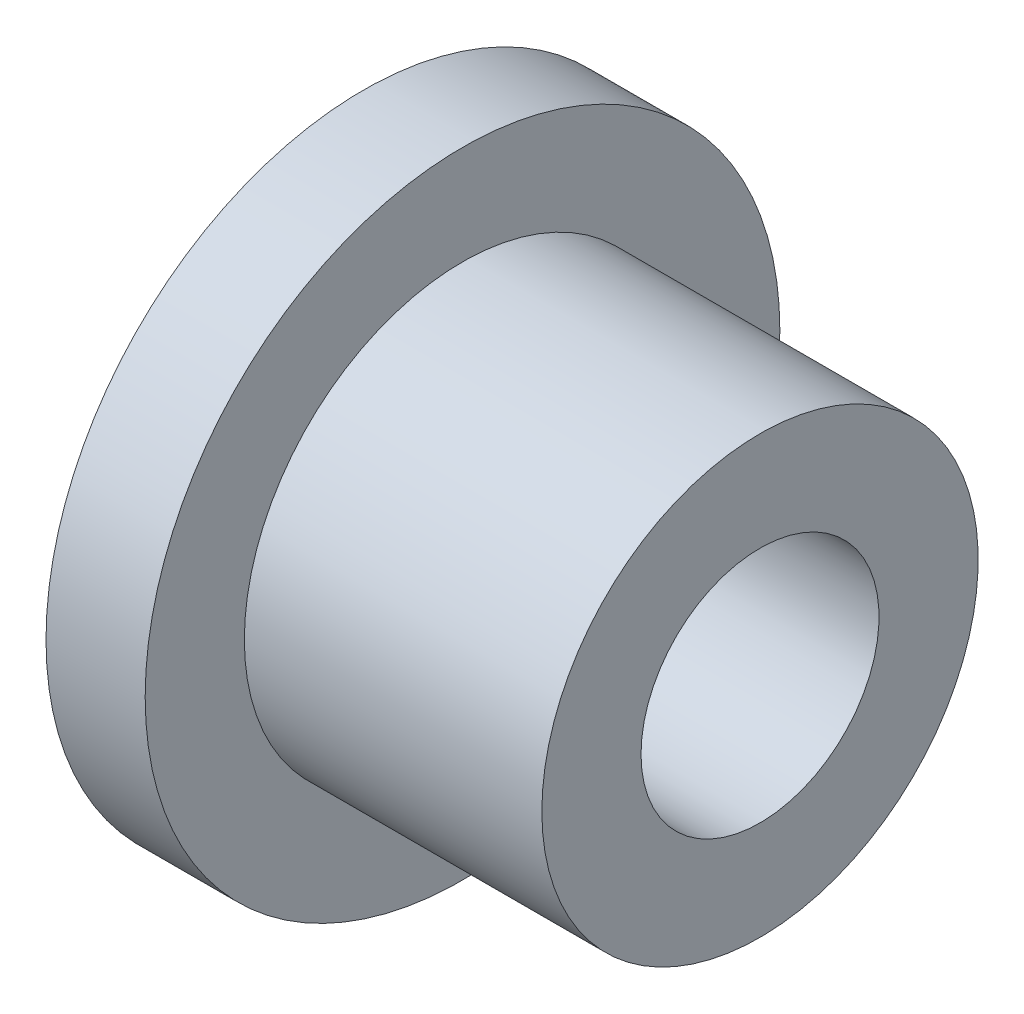
SolidWorks part; units mm, degrees
ref_plane "Front Plane" through (0, 0, 0) normal (0, 0, 1) x (1, 0, 0)
ref_plane "Top Plane" through (0, 0, 0) normal (0, 1, 0) x (1, 0, 0)
ref_plane "Right Plane" through (0, 0, 0) normal (1, 0, 0) x (0, 0, -1)
other "Configuration Table"
sketch "Sketch1" plane through (0, 0, 0) normal (0, 0, 1) x (1, 0, 0)
  line L0 (0, 6) -> (0, 16)
  line L1 (0, 16) -> (5, 16)
  line L2 (5, 16) -> (5, 11)
  line L3 (5, 11) -> (20, 11)
  line L4 (20, 11) -> (20, 6)
  line L5 (20, 6) -> (0, 6)
  line L6 (-20, 0) -> (50, 0) construction
  dimension "D1" = 12
  dimension "D2" = 22
  dimension "D3" = 32
  dimension "D4" = 20
  dimension "D5" = 5
revolve "Revolve1" add sketch "Sketch1" angle 360 about L6
